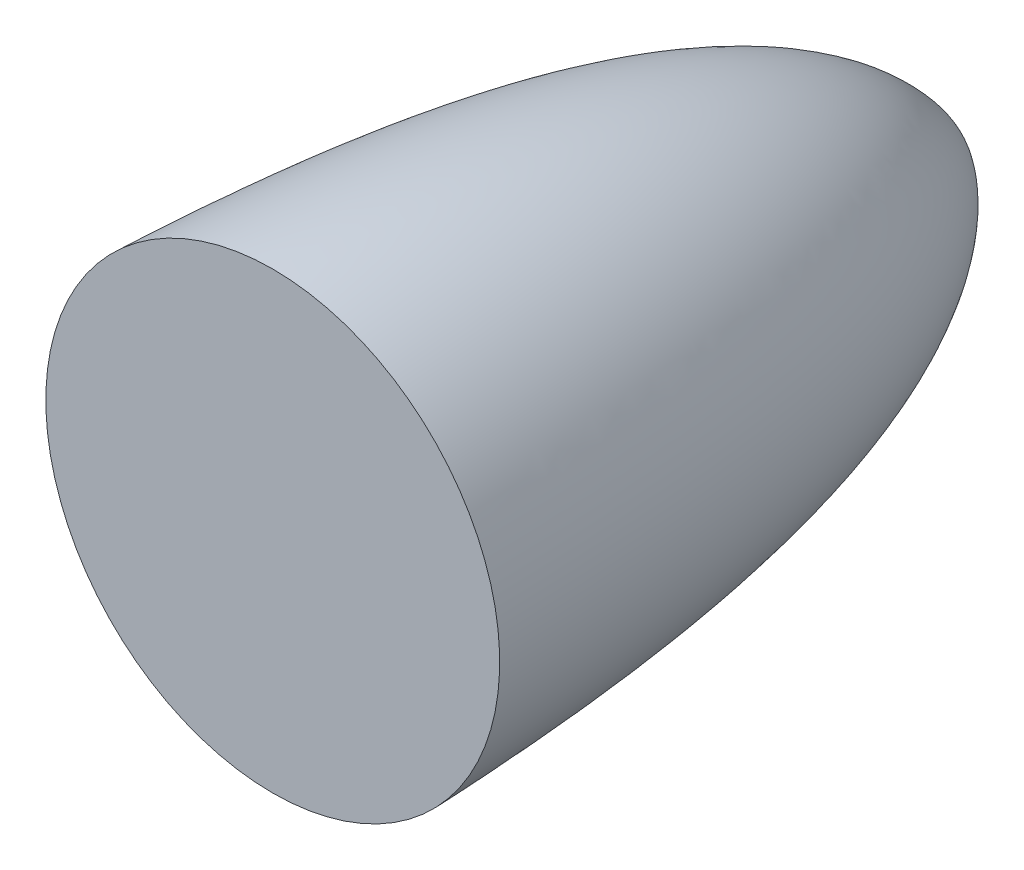
SolidWorks part; units mm, degrees
material "Plain Carbon Steel"
ref_plane "Front Plane" through (0, 0, 0) normal (0, 0, 1) x (1, 0, 0)
ref_plane "Top Plane" through (0, 0, 0) normal (0, 1, 0) x (1, 0, 0)
ref_plane "Right Plane" through (0, 0, 0) normal (1, 0, 0) x (0, 0, -1)
sketch "Sketch1" plane through (0, 0, 0) normal (0, 0, 1) x (1, 0, 0)
  circle A0 centre (0, 0) radius 10
  dimension "D1" = 20
ref_plane "Plane1" through (0, 0, -30) normal (0, 0, 1) x (1, 0, 0)
sketch "Sketch2" plane through (0, 0, -30) normal (0, 0, 1) x (1, 0, 0)
  circle A0 centre (0, 0) radius 0.04
sketch "Sketch3" plane through (0, 0, 0) normal (1, 0, 0) x (0, 0, -1)
  line L1 (30, 0.04) -> (30, -0.04) construction
  line L2 (30, 0) -> (0, 0) construction
  line L3 (0, 0) -> (0, 10) construction
  line L4 (0, 10) -> (0, -10) construction
  line L5 (0, 10) -> (30, 0) construction
  line L6 (0, 10) -> (14.1683, 9.4736) construction
  line L7 (14.1683, 9.4736) -> (24.5042, 7.6746) construction
  line L8 (24.5042, 7.6746) -> (28.789, 3.4879) construction
  line L9 (28.789, 3.4879) -> (30, 0) construction
  line L10 (0, 10) -> (0, 0)
  line L11 (0, 0) -> (30, 0)
  spline S0 degree 4 poles (0, 10) (14.1683, 9.4736) (24.5042, 7.6746) (28.789, 3.4879) (30, 0) knots 0 0 0 0 0 1 1 1 1 1
  dimension "D1" = 10
revolve "Revolve1" add sketch "Sketch3" angle 360 about L11
